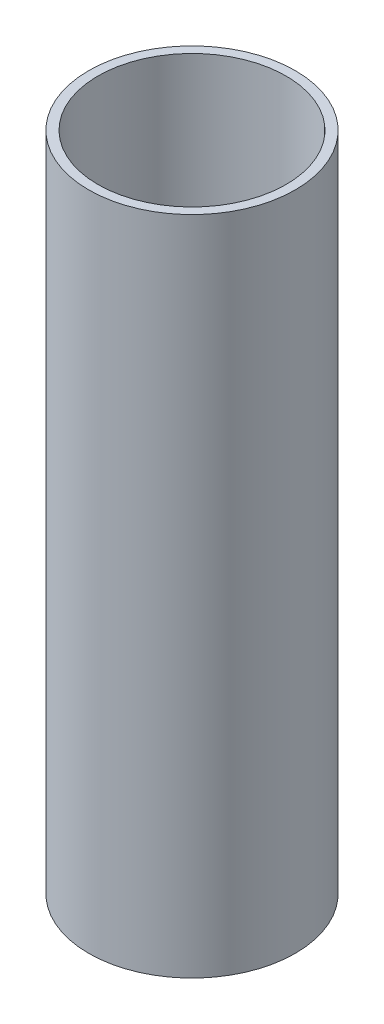
SolidWorks part; units mm, degrees
ref_plane "Front Plane" through (0, 0, 0) normal (0, 0, 1) x (1, 0, 0)
ref_plane "Top Plane" through (0, 0, 0) normal (0, 1, 0) x (1, 0, 0)
ref_plane "Right Plane" through (0, 0, 0) normal (1, 0, 0) x (0, 0, -1)
sketch "Sketch1" plane through (0, 0, 0) normal (0, 1, 0) x (1, 0, 0)
  circle A0 centre (0, 0) radius 7.9375
  circle A1 centre (0, 0) radius 7.2263
  dimension "D1" = 15.875
  dimension "D2" = 14.4526
extrude "Boss-Extrude1" add sketch "Sketch1" along normal blind 50.8
